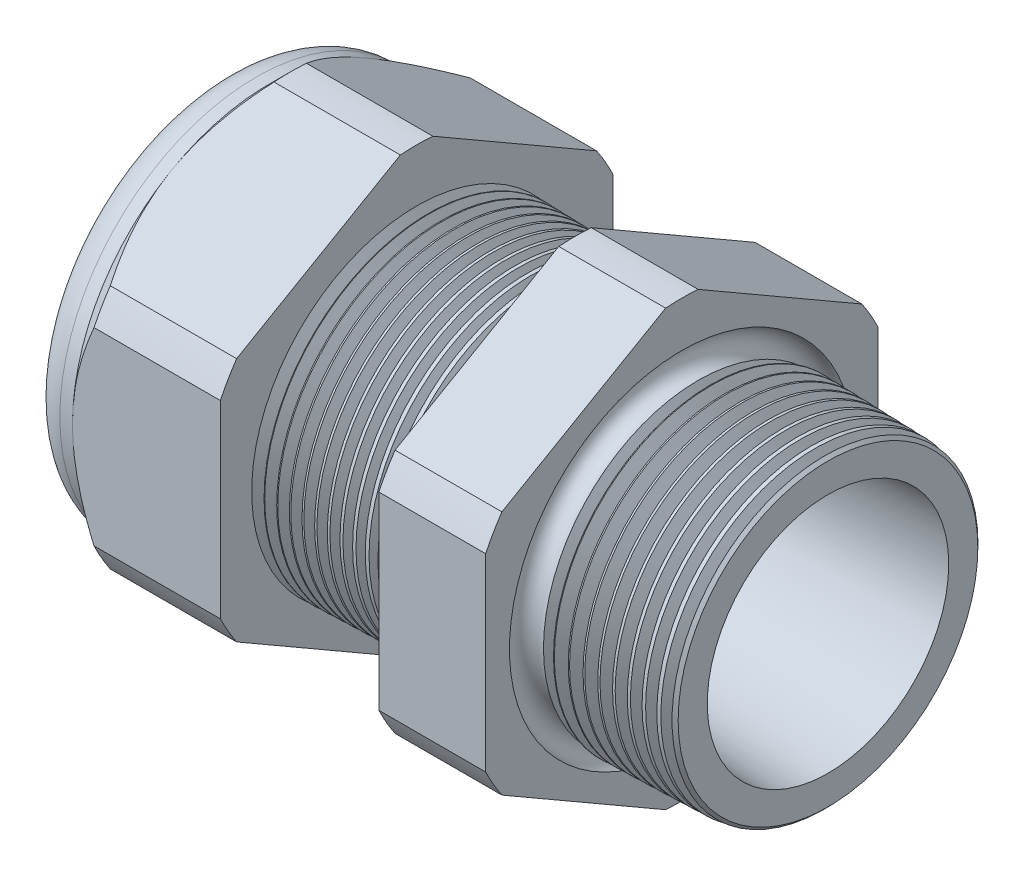
SolidWorks part; units mm, degrees
ref_plane "Front Plane" through (0, 0, 0) normal (0, 0, 1) x (1, 0, 0)
ref_plane "Top Plane" through (0, 0, 0) normal (0, 1, 0) x (1, 0, 0)
ref_plane "Right Plane" through (0, 0, 0) normal (1, 0, 0) x (0, 0, -1)
sketch "Sketch10" plane through (0, 0, 0) normal (0, 0, 1) x (1, 0, 0)
  line L0 (0, 0) -> (-115.3565, 0) construction
  line L1 (-35.814, 5.969) -> (-24.014, 5.969)
  line L2 (1.016, 7.3456) -> (1.016, 9.3776)
  line L3 (-7.874, 9.6104) -> (1.016, 9.3776)
  line L4 (-7.874, 23.876) -> (-7.874, 9.6104)
  line L5 (-7.874, 23.876) -> (-14.374, 23.876)
  line L6 (-14.374, 23.876) -> (-14.374, 9.7806)
  line L7 (-24.014, 10.033) -> (-14.374, 9.7806)
  line L8 (-24.014, 10.033) -> (-24.014, 23.876)
  line L9 (-24.014, 23.876) -> (-33.014, 23.876)
  line L10 (-33.014, 23.876) -> (-33.014, 11.938)
  line L11 (-33.014, 11.938) -> (-35.814, 11.938)
  line L12 (-35.814, 11.938) -> (-35.814, 5.969)
  line L13 (-24.014, 5.969) -> (1.016, 7.3456)
  dimension "D1" = 36.83
  dimension "D2" = 11.938
  dimension "D3" = 1.5
  dimension "D4" = 2.032
  dimension "A" = 20.066
  dimension "D6" = 23.876
  dimension "D8" = 47.752
  dimension "D9" = 2.8
  dimension "D10" = 9
  dimension "D11" = 6.5
  dimension "D" = 8.89
revolve "Revolve2" add sketch "Sketch10" angle 360 about L0
sketch "Sketch12" plane through (-33.014, 0, 0) normal (-1, 0, 0) x (0, 0, 1)
  line L1 (-0.9882, 13.2143) -> (-10.9498, 7.4629)
  line L2 (-11.938, 5.7513) -> (-11.938, -5.7513)
  line L3 (-10.9498, -7.4629) -> (-0.9882, -13.2143)
  line L4 (0.9882, -13.2143) -> (10.9498, -7.4629)
  line L5 (11.938, -5.7513) -> (11.938, 5.7513)
  line L6 (10.9498, 7.4629) -> (0.9882, 13.2143)
  circle A0 centre (0, 0) radius 11.938 construction
  arc A1 (0.9882, 13.2143) -> (-0.9882, 13.2143) centre (0, 0) ccw
  arc A2 (-10.9498, 7.4629) -> (-11.938, 5.7513) centre (0, 0) ccw
  arc A3 (-11.938, -5.7513) -> (-10.9498, -7.4629) centre (0, 0) ccw
  arc A4 (-0.9882, -13.2143) -> (0.9882, -13.2143) centre (0, 0) ccw
  arc A5 (10.9498, -7.4629) -> (11.938, -5.7513) centre (0, 0) ccw
  arc A6 (11.938, 5.7513) -> (10.9498, 7.4629) centre (0, 0) ccw
  dimension "D2" = 26.5024
  dimension "D1" = 23.876
extrude "Cut-Extrude2" cut sketch "Sketch12" against normal through all flip side to cut
fillet "Fillet4" radius 2.032 1 edges at (-35.814, 0, -11.938)
sketch "Sketch19" plane through (-33.014, 0, 0) normal (-1, 0, 0) x (0, 0, 1)
  line L0 (11.938, 0) -> (11.938, 5.7513) construction
  circle A0 centre (0, 0) radius 11.938
extrude "Cut-Extrude3" cut sketch "Sketch19" against normal blind 2 draft 45 flip side to cut
chamfer "Chamfer1" distance 0.254 angle 45 1 edges at (1.016, 0, -9.3776)
sketch "Sketch21" plane through (-35.814, 0, 0) normal (-1, 0, 0) x (0, 0, 1)
  circle A0 centre (0, 0) radius 5.969
  circle A2 centre (0, 0) radius 5.969 construction
extrude "plug" add sketch "Sketch21" against normal blind 6.35 separate body
sketch "Sketch22" plane through (-35.814, 0, 0) normal (-1, 0, 0) x (0, 0, 1)
  circle A0 centre (0, 0) radius 5.715
  circle A1 centre (0, 0) radius 5.969 construction
  dimension "D1" = 0.254
extrude "Cut-Extrude4" cut sketch "Sketch22" against normal blind 0.508
sketch "Sketch27" plane through (-35.306, 0, 0) normal (-1, 0, 0) x (0, 0, 1)
  line L0 (-4.3624, 0) -> (4.3624, 0) construction
  circle A0 centre (-4.1849, 0) radius 1.524
  circle A1 centre (0, 0) radius 5.715 construction
  dimension "D1" = 0.0061
  dimension "holedia" = 3.048
extrude "plugholes" cut sketch "Sketch27" against normal through all
pattern_circular "CirPattern1" count 4 over 360 about axis through (0, 0, 0) along (1, 0, 0) of "plugholes"
sketch "Sketch28" [suppressed] plane through (-29.464, 0, 0) normal (-1, 0, 0) x (0, 0, 1)
  circle A0 centre (0, 0) radius 0.762
  dimension "midholedia" = 3.048
extrude "midhole" [suppressed] cut sketch "Sketch28" against normal through all
sketch "Sketch29" plane through (0, 0, 0) normal (0, 0, 1) x (1, 0, 0)
  line L0 (-24.014, 10.033) -> (-23.281, 10.0138)
  line L1 (-14.374, 9.7806) -> (-24.014, 10.033) construction
  line L2 (-23.281, 10.0138) -> (-23.6641, 9.3886)
  line L3 (-23.6641, 9.3886) -> (-24.014, 10.033)
  dimension "D1" = 60
  dimension "D2" = 60
  dimension "D3" = 0.635
revolve "Cut-Revolve1" cut sketch "Sketch29" angle 360 about axis through (0, 0, 0) along (-1, 0, 0)
pattern_linear "LPattern1" count 13 spacing 0.762 along (1, 0, 0) of "Cut-Revolve1"
sketch "Sketch30" plane through (0, 0, 0) normal (0, 0, 1) x (1, 0, 0)
  line L0 (-7.874, 9.6104) -> (-6.9944, 9.5873)
  line L1 (-7.874, 13.2143) -> (-7.874, 7.4629) construction
  line L2 (0.7621, 9.3842) -> (-7.874, 9.6104) construction
  line L3 (-6.9944, 9.5873) -> (-7.4542, 8.8371)
  line L4 (-7.4542, 8.8371) -> (-7.874, 9.6104)
  dimension "D1" = 60
  dimension "D2" = 60
  dimension "D3" = 0.762
revolve "Cut-Revolve2" cut sketch "Sketch30" angle 360 about axis through (0, 0, 0) along (-1, 0, 0)
pattern_linear "LPattern2" count 10 spacing 0.889 along (1, 0, 0) of "Cut-Revolve2"
sketch "Sketch31" [suppressed] plane through (-38.354, 0, 0) normal (-1, 0, 0) x (0, 0, 1)
  line L0 (-1.905, 1.905) -> (1.905, 1.905)
  line L1 (-1.905, -1.905) -> (1.905, -1.905)
  circle A0 centre (0, 0) radius 1.905 construction
  arc A1 (-1.905, 1.905) -> (-1.905, -1.905) centre (-1.905, 0) ccw
  arc A2 (1.905, 1.905) -> (1.905, -1.905) centre (1.905, 0) cw
extrude "Cut-Extrude5" [suppressed] cut sketch "Sketch31" against normal through all
sketch "Sketch32" plane through (0, 0, 0) normal (0, 0, 1) x (1, 0, 0)
  line L0 (-7.874, 13.2143) -> (-7.874, 7.4629) construction
  circle A0 centre (-7.747, 9.6104) radius 0.889
  dimension "D2" = 1.778
  dimension "D1" = 0.127
revolve "Cut-Revolve3" cut sketch "Sketch32" angle 360 about axis through (0, 0, 0) along (-1, 0, 0)
